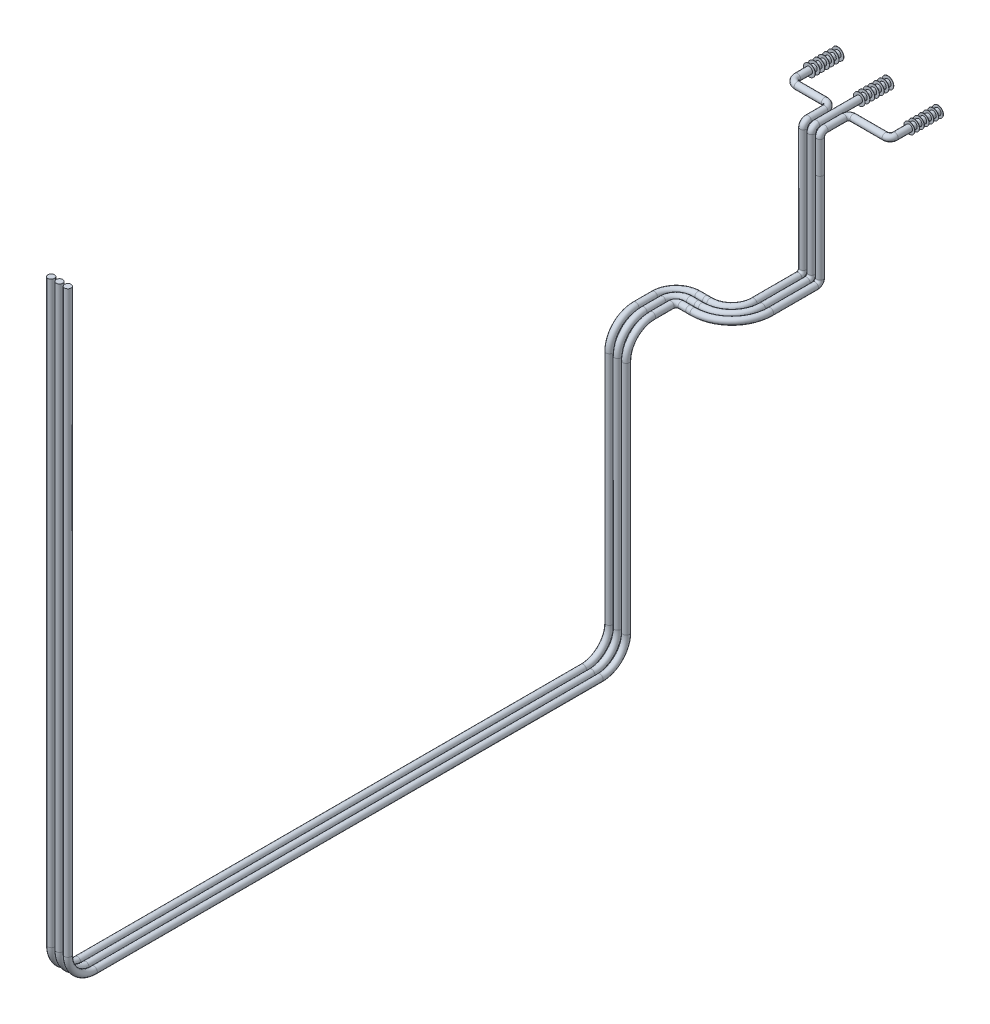
SolidWorks part; units mm, degrees
ref_plane "Alzado" through (0, 0, 0) normal (0, 0, 1) x (1, 0, 0)
ref_plane "Planta" through (0, 0, 0) normal (0, 1, 0) x (1, 0, 0)
ref_plane "Vista lateral" through (0, 0, 0) normal (1, 0, 0) x (0, 0, -1)
sketch "Croquis1" plane through (0, 0, 0) normal (0, 0, 1) x (1, 0, 0)
  line L0 (0, 0) -> (210, 0) construction
  line L1 (210, 0) -> (420, 0) construction
  circle A0 centre (0, 0) radius 13.7
  circle A1 centre (210, 0) radius 13.7
  circle A2 centre (210, 0) radius 13.7
  dimension "D1" = 27.4
  dimension "D3" = 27.4
  dimension "D2" = 210
  dimension "D4" = 210
sketch3d "Croquis3D1"
  line L0 (0, 0, 0) -> (0, 0, 170)
  line L1 (30, 0, 200) -> (145.0002, 0, 200)
  line L2 (175.0002, 0, 230) -> (175.0002, 0, 300)
  line L3 (175.0002, -20, 320) -> (175.0002, -156.8001, 320)
  arc A0 (0, 0, 170) -> (30, 0, 200) centre (30, 0, 170) ccw
  arc A1 (145.0002, 0, 200) -> (175.0002, 0, 230) centre (145.0002, 0, 230) ccw
  arc A2 (175.0002, 0, 300) -> (175.0002, -20, 320) centre (175.0002, -20, 300) ccw
  point P10 (0, 0, 200)
  point P11 (30, 30, 170)
  point P14 (175.0002, 0, 200)
  point P15 (145.0002, -30, 230)
  point P19 (175.0002, 0, 320)
  point P20 (195.0002, -20, 300)
  dimension "D1" = 30
  dimension "D2" = 20
  dimension "D3" = 175.0002
  dimension "D4" = 200
  dimension "D5" = 120
sweep "Barrer5" add path "Croquis3D1" circular profile diameter 27.4 parameters "D3"=27.4
sketch "Croquis14" plane through (0, 0, 0) normal (0, 0, 1) x (1, 0, 0)
  circle A0 centre (210, 0) radius 13.7
sketch3d "Croquis3D2"
  line L0 (210, 0, 0) -> (210, 0, 299.997)
  line L1 (210, -20, 319.997) -> (210, -153.4253, 319.997)
  arc A0 (210, 0, 299.997) -> (210, -20, 319.997) centre (210, -20, 299.997) ccw
  point P8 (210, 0, 319.997)
  point P9 (230, -20, 299.997)
  dimension "D1" = 20
  dimension "D2" = 319.997
sweep "Barrer6" add path "Croquis3D2" circular profile diameter 27.4 parameters "D3"=27.4
sketch "Croquis41" plane through (0, 0, 0) normal (0, 0, -1) x (-1, 0, 0)
  circle A0 centre (-420, 0) radius 13.7
  dimension "D1" = 27.4
sketch3d "Croquis3D3"
  line L0 (420, 0, 0) -> (420, 0, 180)
  line L1 (400, 0, 200) -> (264.998, 0, 200)
  line L2 (244.998, 0, 220) -> (244.998, 0, 300)
  line L3 (244.998, -20, 320) -> (244.998, -158.8149, 320)
  arc A0 (244.998, 0, 300) -> (244.998, -20, 320) centre (244.998, -20, 300) ccw
  arc A1 (420, 0, 180) -> (400, 0, 200) centre (400, 0, 180) ccw
  arc A2 (264.998, 0, 200) -> (244.998, 0, 220) centre (264.998, 0, 220) ccw
  point P8 (244.998, 0, 320)
  point P9 (264.998, -20, 300)
  point P12 (420, 0, 200)
  point P13 (400, -20, 180)
  point P16 (244.998, 0, 200)
  point P17 (264.998, 20, 220)
  dimension "D1" = 20
  dimension "D2" = 175.002
  dimension "D3" = 200
  dimension "D4" = 120
sweep "Barrer7" add profiles "Croquis41" path "Croquis3D3"
sketch "Croquis62" plane through (0, 0, 0) normal (0, 0, -1) x (-1, 0, 0)
  circle A0 centre (-420, 0) radius 22.8702
  circle A1 centre (-210, 0) radius 24.3657
  circle A2 centre (0, 0) radius 24.738
extrude "Saliente-Extruir1" add sketch "Croquis62" along normal blind 1
pattern_linear "MatrizL1" count 7 spacing 20 along (0, 0, 1) of "Saliente-Extruir1"
sketch "Croquis64" plane through (0, -158.8149, 0) normal (0, -1, 0) x (1, 0, 0)
  line L1 (71.8798, 336.7936) -> (310.9459, 336.7936)
  line L2 (71.8798, 336.7936) -> (71.8798, 303.5924)
  line L3 (71.8798, 303.5924) -> (310.9459, 303.5924)
  line L4 (310.9459, 336.7936) -> (310.9459, 303.5924)
  line L5 (71.8798, 336.7936) -> (310.9459, 303.5924) construction
  line L6 (71.8798, 303.5924) -> (310.9459, 336.7936) construction
  point P0 (191.4129, 320.193)
extrude "Cortar-Extruir1" cut sketch "Croquis64" against normal blind 5
sketch "Croquis65" plane through (0, -153.4253, 0) normal (0, -1, 0) x (1, 0, 0)
  circle A0 centre (175.0002, 320) radius 13.7
  circle A1 centre (210, 319.997) radius 13.7
  circle A2 centre (244.998, 320) radius 13.697
sketch3d "Croquis3D4"
  line L0 (175.0002, -153.4253, 320) -> (175.0002, -531.3553, 320)
  line L1 (175.0002, -551.3553, 340) -> (175.0002, -551.3553, 528)
  line L2 (83.0002, -551.3553, 620) -> (65.0002, -551.3553, 620)
  line L3 (65.0002, -551.3553, 620) -> (33.0002, -551.3553, 620)
  line L4 (-58.9998, -551.3553, 712) -> (-58.9998, -551.3553, 790.1856)
  line L5 (-58.9998, -661.3553, 900.1856) -> (-58.9998, -1649.4481, 900.1856)
  line L6 (-58.9998, -1759.4481, 1010.1856) -> (-58.9998, -1759.4481, 3135.1984)
  line L7 (-58.9998, -1649.4481, 3245.1984) -> (-58.9998, 782.6223, 3245.1984)
  arc A0 (33.0002, -551.3553, 620) -> (-58.9998, -551.3553, 712) centre (33.0002, -551.3553, 712) ccw
  arc A1 (-58.9998, -661.3553, 900.1856) -> (-58.9998, -551.3553, 790.1856) centre (-58.9998, -661.3553, 790.1856) ccw
  arc A2 (175.0002, -531.3553, 320) -> (175.0002, -551.3553, 340) centre (175.0002, -531.3553, 340) ccw
  arc A3 (175.0002, -551.3553, 528) -> (83.0002, -551.3553, 620) centre (83.0002, -551.3553, 528) ccw
  arc A4 (-58.9998, -1649.4481, 900.1856) -> (-58.9998, -1759.4481, 1010.1856) centre (-58.9998, -1649.4481, 1010.1856) ccw
  arc A5 (-58.9998, -1759.4481, 3135.1984) -> (-58.9998, -1649.4481, 3245.1984) centre (-58.9998, -1649.4481, 3135.1984) ccw
  point P8 (-58.9998, -551.3553, 620)
  point P9 (33.0002, -459.3553, 712)
  point P14 (-58.9998, -551.3553, 900.1856)
  point P16 (-168.9998, -661.3553, 790.1856)
  point P17 (-94.682, -551.3553, 620)
  point P21 (175.0002, -551.3553, 320)
  point P22 (155.0002, -531.3553, 340)
  point P26 (175.0002, -551.3553, 620)
  point P27 (83.0002, -643.3553, 528)
  point P28 (-58.9998, -1759.4481, 900.1856)
  point P29 (-168.9998, -1649.4481, 1010.1856)
  point P33 (-58.9998, -1759.4481, 3245.1984)
  point P34 (-168.9998, -1649.4481, 3135.1984)
  dimension "D3" = 110
  dimension "D4" = 92
  dimension "D6" = 110
  dimension "D8" = 92
  dimension "D7" = 110
  dimension "D11" = 110
  dimension "D1" = 397.93
  dimension "D2" = 300
  dimension "D5" = 50
  dimension "D9" = 1208.0928
  dimension "D10" = 2345.0128
  dimension "D12" = 2542.0704
sweep "Barrer10" add profiles "Croquis65" path "Croquis3D4"
